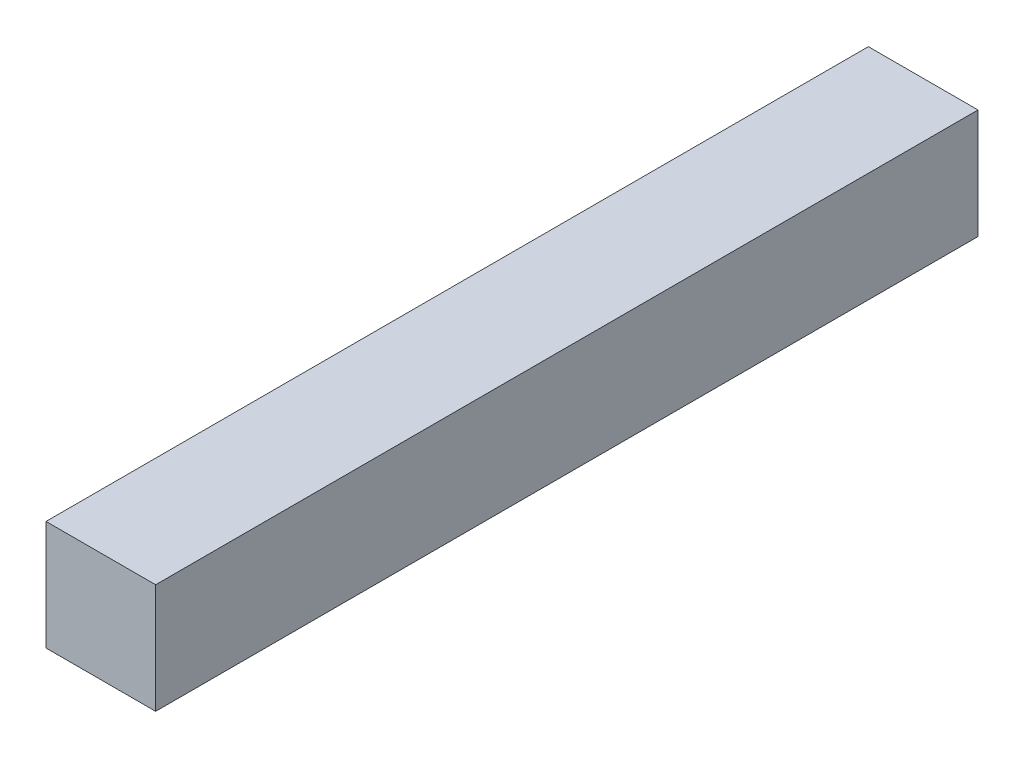
SolidWorks part; units mm, degrees
ref_plane "Front Plane" through (0, 0, 0) normal (0, 0, 1) x (1, 0, 0)
ref_plane "Top Plane" through (0, 0, 0) normal (0, 1, 0) x (1, 0, 0)
ref_plane "Right Plane" through (0, 0, 0) normal (1, 0, 0) x (0, 0, -1)
sketch "Sketch7" plane through (0, 0, 0) normal (0, 0, 1) x (1, 0, 0)
  line L1 (-10.16, -10.16) -> (10.16, -10.16)
  line L2 (-10.16, -10.16) -> (-10.16, 10.16)
  line L3 (-10.16, 10.16) -> (10.16, 10.16)
  line L4 (10.16, -10.16) -> (10.16, 10.16)
  line L5 (-10.16, -10.16) -> (10.16, 10.16) construction
  line L6 (-10.16, 10.16) -> (10.16, -10.16) construction
  point P0 (0, 0)
  dimension "D1" = 20.32
extrude "Boss-Extrude3" add sketch "Sketch7" along normal mid plane 152.4
